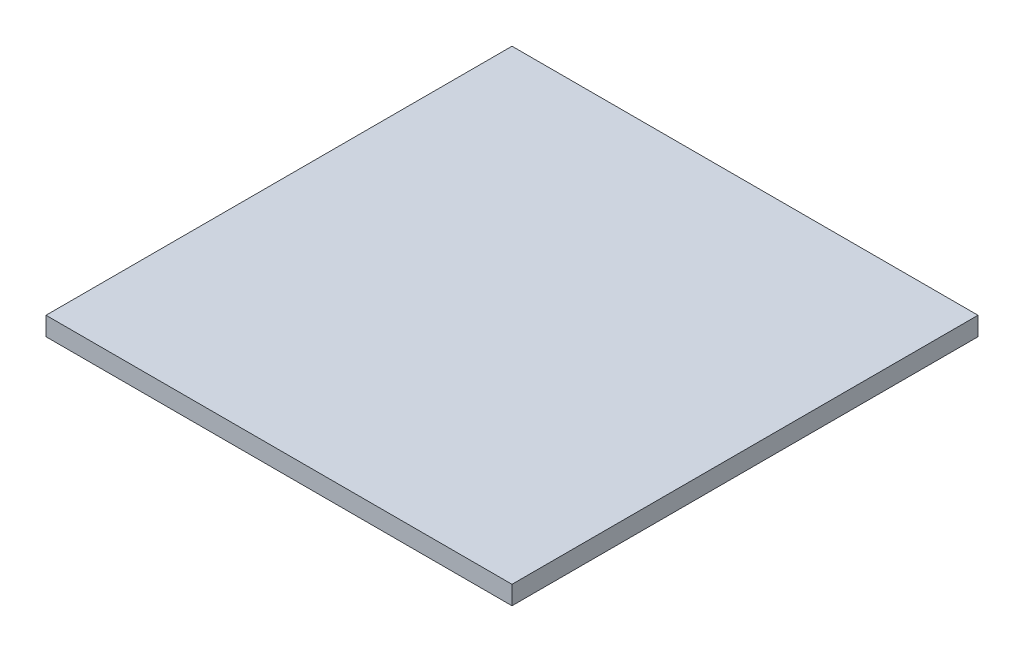
SolidWorks part; units mm, degrees
ref_plane "前视基准面" through (0, 0, 0) normal (0, 0, 1) x (1, 0, 0)
ref_plane "上视基准面" through (0, 0, 0) normal (0, 1, 0) x (1, 0, 0)
ref_plane "右视基准面" through (0, 0, 0) normal (1, 0, 0) x (0, 0, -1)
sketch "草图1" plane through (0, 0, 0) normal (0, 1, 0) x (1, 0, 0)
  line L1 (-25, -25) -> (25, -25)
  line L2 (-25, -25) -> (-25, 25)
  line L3 (-25, 25) -> (25, 25)
  line L4 (25, -25) -> (25, 25)
  line L5 (-25, -25) -> (25, 25) construction
  line L6 (-25, 25) -> (25, -25) construction
  point P0 (0, 0)
  dimension "D1" = 50
  dimension "D2" = 50
extrude "凸台-拉伸1" add sketch "草图1" along normal blind 2
